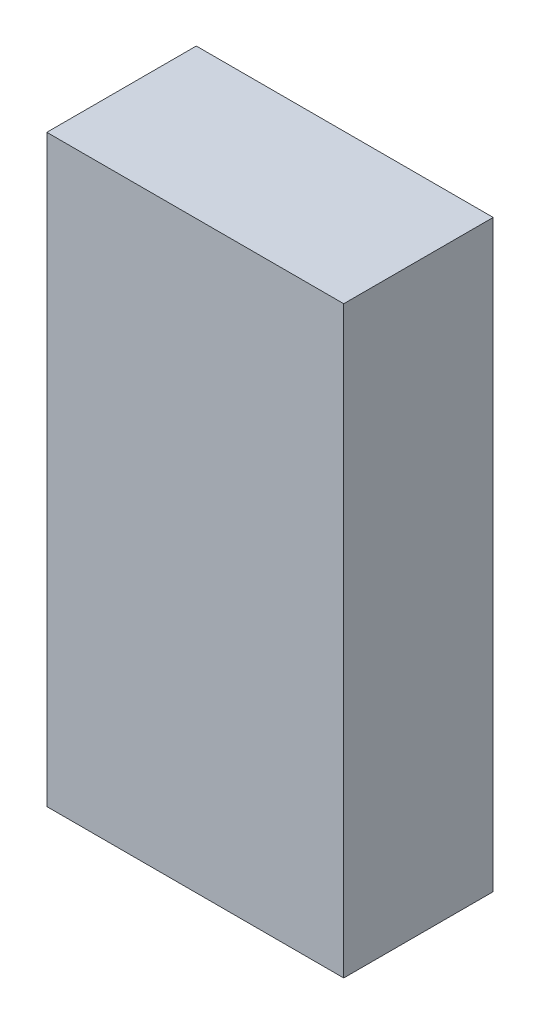
SolidWorks part; units mm, degrees
ref_plane "Plan de face" through (0, 0, 0) normal (0, 0, 1) x (1, 0, 0)
ref_plane "Plan de dessus" through (0, 0, 0) normal (0, 1, 0) x (1, 0, 0)
ref_plane "Plan de droite" through (0, 0, 0) normal (1, 0, 0) x (0, 0, -1)
sketch "Esquisse1" plane through (0, 0, 0) normal (0, 0, 1) x (1, 0, 0)
  line L1 (-96.0625, 65.0087) -> (-10.6425, 65.0087)
  line L2 (-96.0625, 65.0087) -> (-96.0625, -102.9913)
  line L3 (-96.0625, -102.9913) -> (-10.6425, -102.9913)
  line L4 (-10.6425, 65.0087) -> (-10.6425, -102.9913)
  dimension "D1" = 168
  dimension "D2" = 85.42
extrude "Boss.-Extru.1" add sketch "Esquisse1" along normal blind 43
